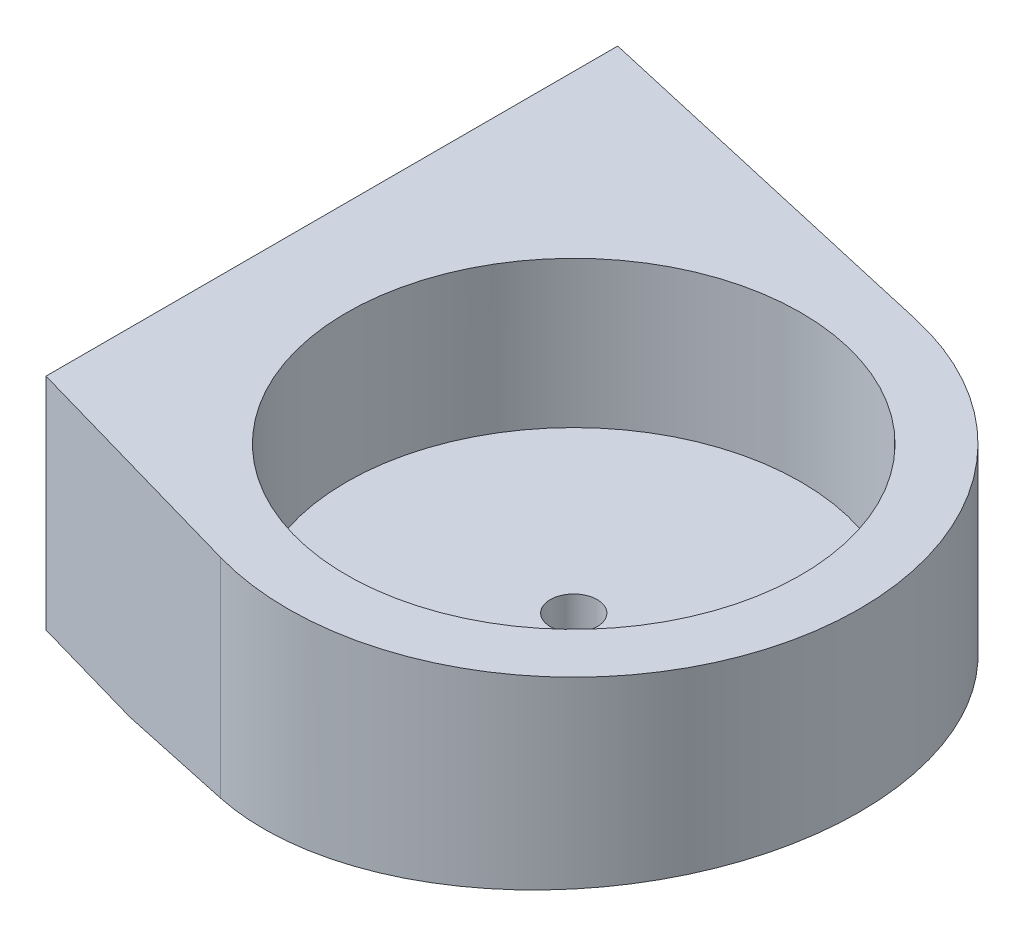
SolidWorks part; units mm, degrees
ref_plane "Front" through (0, 0, 0) normal (0, 0, 1) x (1, 0, 0)
ref_plane "Top" through (0, 0, 0) normal (0, 1, 0) x (1, 0, 0)
ref_plane "Right" through (0, 0, 0) normal (1, 0, 0) x (0, 0, -1)
sketch "Sketch1" plane through (0, 0, 0) normal (0, 1, 0) x (1, 0, 0)
  circle A0 centre (0, 0) radius 15.5
  dimension "D1" = 31
extrude "Boss-Extrude1" add sketch "Sketch1" along normal blind 5
sketch "Sketch2" plane through (0, 0, 0) normal (0, -1, 0) x (1, 0, 0)
  line L0 (-5.3514, 18.7513) -> (-22, 14)
  line L1 (-22, 14) -> (-22, -25)
  line L2 (-22, -25) -> (4.3235, -19.0147)
  circle A3 centre (0, 0) radius 19.5
  arc A4 (4.3235, -19.0147) -> (-5.3514, 18.7513) centre (0, 0) ccw
  circle M5 centre (0, 0) radius 15.5
  dimension "D4" = 14
  dimension "D2" = 22
  dimension "D3" = 39
  dimension "D1" = 4
extrude "Boss-Extrude2" add sketch "Sketch2" against normal blind 15 contours L2 A4 L0 L1 M5
sketch "Sketch17" plane through (0, 0, 0) normal (0, 0, 1) x (1, 0, 0)
  line L0 (-22, 0) -> (-14, 0)
  line L1 (-5.3514, 0) -> (-22, 0) construction
  line L2 (-14, 0) -> (19.5, 3)
  line L3 (19.5, 0) -> (19.5, 15) construction
  line L4 (19.5, 3) -> (19.5, 0)
  line L5 (19.5, 0) -> (-14, 0)
  line L6 (19.5, 15) -> (-5.3514, 15) construction
  dimension "D1" = 8
  dimension "D2" = 12
extrude "Cut-Extrude7" cut sketch "Sketch17" against normal through all and the other way through all contours L5 L4 L2
sketch "Sketch18" plane through (0, 5, 0) normal (0, 1, 0) x (1, 0, 0)
  circle A0 centre (0, 0) radius 1.6
  dimension "D1" = 3.2
extrude "Cut-Extrude8" cut sketch "Sketch18" against normal through all contours A0
sketch "Sketch19" plane through (0, 0, 0) normal (0, -1, 0) x (1, 0, 0)
  line L0 (-22, -5.5) -> (-18, -5.5) construction
  line L1 (-22, 14) -> (-22, -25) construction
  circle A0 centre (-18, -5.5) radius 2.05
  dimension "D2" = 4.1
  dimension "D1" = 4
extrude "Cut-Extrude9" cut sketch "Sketch19" against normal blind 6
ref_plane "Plane5" through (0, 2, 0) normal (0, 1, 0) x (1, 0, 0)
sketch "Sketch20" plane through (0, 2, 0) normal (0, 1, 0) x (1, 0, 0)
  circle A0 centre (0, 0) radius 4
  dimension "D1" = 8
extrude "Cut-Extrude10" cut sketch "Sketch20" against normal up to next
